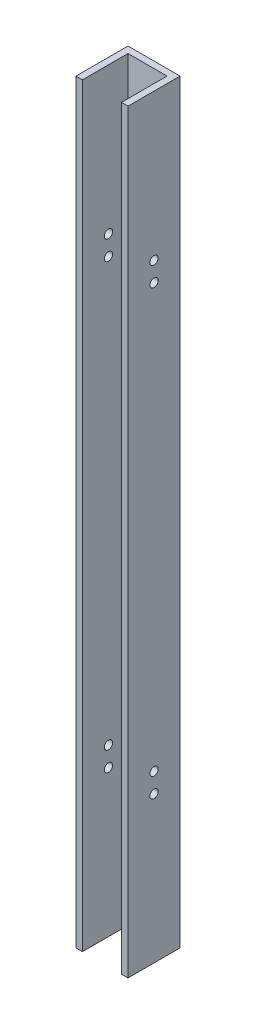
SolidWorks part; units mm, degrees
material "Plain Carbon Steel"
ref_plane "Front Plane" through (0, 0, 0) normal (0, 0, 1) x (1, 0, 0)
ref_plane "Top Plane" through (0, 0, 0) normal (0, 1, 0) x (1, 0, 0)
ref_plane "Right Plane" through (0, 0, 0) normal (1, 0, 0) x (0, 0, -1)
sketch "Sketch1" plane through (0, 0, 0) normal (0, 1, 0) x (1, 0, 0)
  line L0 (0, 0) -> (3.175, 0)
  line L1 (0, 0) -> (0, 25.4)
  line L2 (0, 25.4) -> (25.4, 25.4)
  line L3 (25.4, 25.4) -> (25.4, 0)
  line L4 (25.4, 0) -> (22.225, 0)
  line L5 (22.225, 0) -> (22.225, 22.225)
  line L6 (22.225, 22.225) -> (3.175, 22.225)
  line L7 (3.175, 22.225) -> (3.175, 0)
extrude "Boss-Extrude1" add sketch "Sketch1" along normal blind 368.3 contours L2 L3 L4 L5 L6 L7 L0 L1
sketch "Sketch2" plane through (0, 0, 0) normal (-1, 0, 0) x (0, 0, 1)
  circle A0 centre (-12.7, 71.4375) radius 2.032
  circle A1 centre (-12.7, 296.8625) radius 2.032
  circle A4 centre (-12.7, 287.3375) radius 2.032
  circle A5 centre (-12.7, 80.9625) radius 2.032
  point P7 (0, 0)
extrude "Cut-Extrude1" cut sketch "Sketch2" against normal blind 25.4
